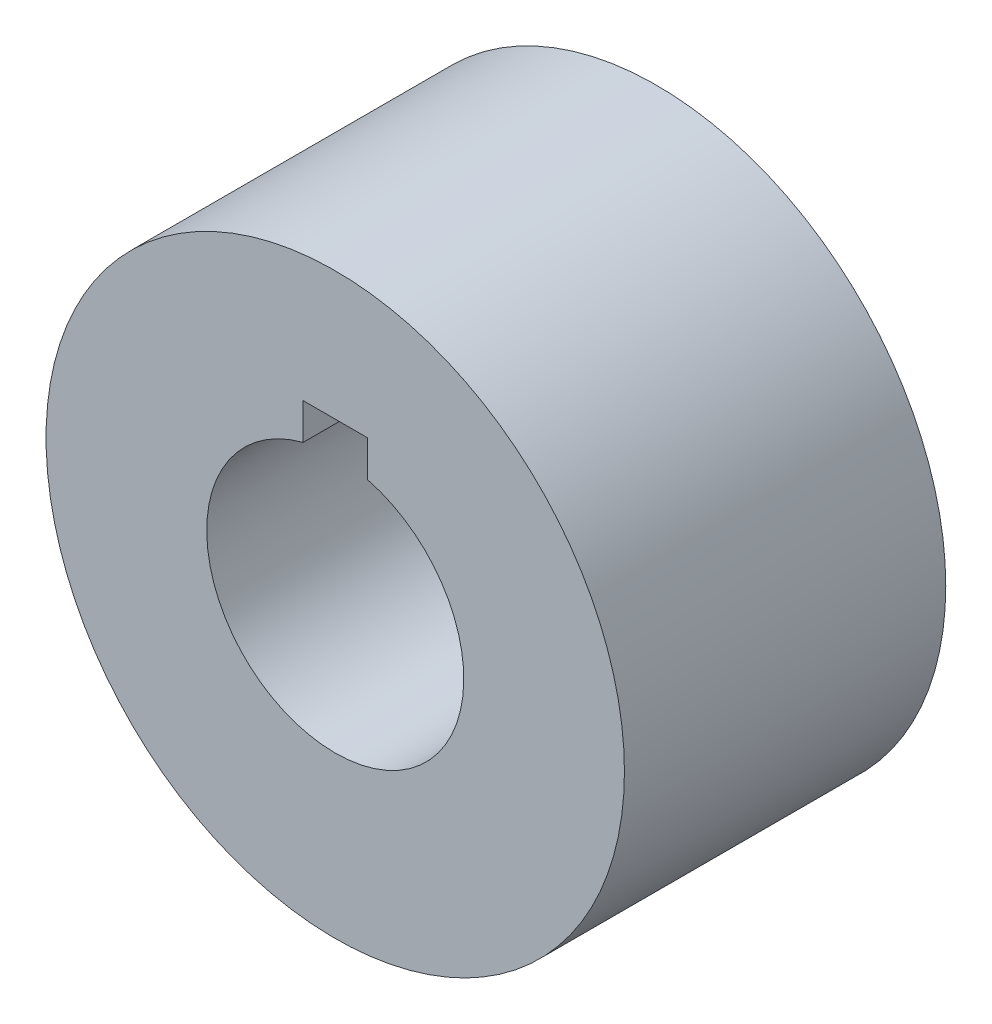
SolidWorks part; units mm, degrees
ref_plane "正面" through (0, 0, 0) normal (0, 0, 1) x (1, 0, 0)
ref_plane "平面" through (0, 0, 0) normal (0, 1, 0) x (1, 0, 0)
ref_plane "右側面" through (0, 0, 0) normal (1, 0, 0) x (0, 0, -1)
sketch "ｽｹｯﾁ1" plane through (0, 0, 0) normal (0, 0, 1) x (1, 0, 0)
  line L0 (-1, 5) -> (-1, 3.873)
  line L1 (-1, 3) -> (1, 3) construction
  line L2 (-1, 3) -> (-1, 5) construction
  line L3 (-1, 5) -> (1, 5) construction
  line L4 (1, 3) -> (1, 5) construction
  line L5 (-1, 3) -> (1, 5) construction
  line L6 (-1, 5) -> (1, 3) construction
  line L7 (-1, 5) -> (1, 5)
  line L8 (1, 5) -> (1, 3.873)
  arc A0 (-1, 3.873) -> (1, 3.873) centre (0, 0) ccw
  circle A1 centre (0, 0) radius 9
  point P4 (0, 4)
  dimension "D1" = 8
  dimension "D2" = 18
  dimension "D3" = 3
  dimension "D4" = 2
extrude "ﾎﾞｽ - 押し出し1" add sketch "ｽｹｯﾁ1" along normal blind 10
